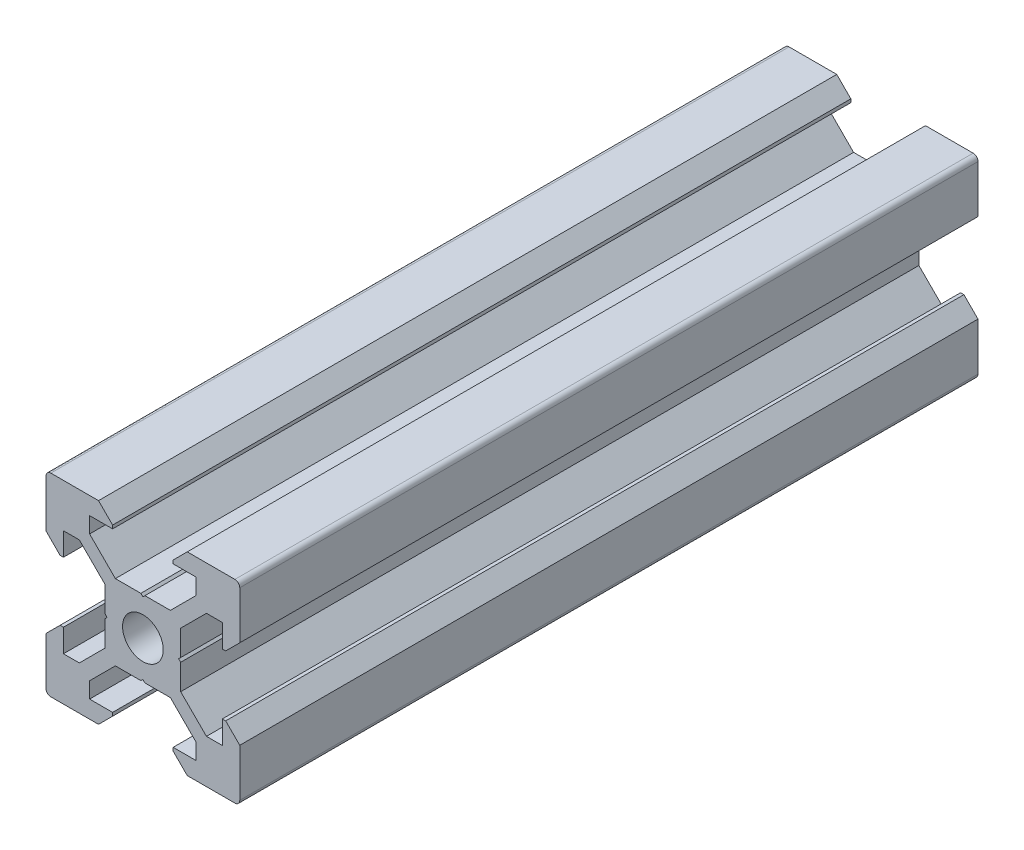
SolidWorks part; units mm, degrees
material "6061-T6 (SS)"
ref_plane "Front Plane" through (0, 0, 0) normal (0, 0, 1) x (1, 0, 0)
ref_plane "Top Plane" through (0, 0, 0) normal (0, 1, 0) x (1, 0, 0)
ref_plane "Right Plane" through (0, 0, 0) normal (1, 0, 0) x (0, 0, -1)
sketch "Sketch1" plane through (0, 0, 0) normal (0, 0, 1) x (1, 0, 0)
  line L1 (9.5, -10) -> (-9.5, -10)
  line L2 (10, -9.5) -> (10, 9.5)
  line L3 (9.5, 10) -> (-9.5, 10)
  line L4 (-10, -9.5) -> (-10, 9.5)
  line L5 (10, -10) -> (-10, 10) construction
  line L6 (10, 10) -> (-10, -10) construction
  circle A0 centre (0, 0) radius 2.1
  arc A1 (-9.5, 10) -> (-10, 9.5) centre (-9.5, 9.5) ccw
  arc A2 (10, 9.5) -> (9.5, 10) centre (9.5, 9.5) ccw
  arc A3 (9.5, -10) -> (10, -9.5) centre (9.5, -9.5) ccw
  arc A4 (-9.5, -10) -> (-10, -9.5) centre (-9.5, -9.5) cw
  point P0 (0, 0)
  line B0 (0, 0) -> (0, 10) construction
  line B1 (0, 3.69) -> (-0.21, 3.9)
  line B2 (-0.21, 3.9) -> (-2.8393, 3.9)
  line B3 (-2.8393, 3.9) -> (-5.5, 6.5607)
  line B4 (-5.5, 6.5607) -> (-5.5, 8.2)
  line B5 (-5.5, 8.2) -> (-3.125, 8.2)
  line B6 (-3.125, 8.2) -> (-3.125, 8.545)
  line B7 (-3.125, 8.545) -> (-4.58, 10)
  line B8 (-4.58, 10) -> (4.58, 10)
  line B9 (0, 0) -> (-5.9132, 5.9132) construction
  line B10 (3.125, 8.545) -> (4.58, 10)
  line B11 (3.125, 8.2) -> (3.125, 8.545)
  line B12 (5.5, 8.2) -> (3.125, 8.2)
  line B13 (5.5, 6.5607) -> (5.5, 8.2)
  line B14 (2.8393, 3.9) -> (5.5, 6.5607)
  line B15 (0.21, 3.9) -> (2.8393, 3.9)
  line B16 (0, 3.69) -> (0.21, 3.9)
  line B17 (0, 0) -> (-10, 0) construction
  line B18 (-3.69, 0) -> (-3.9, -0.21)
  line B19 (-3.9, -0.21) -> (-3.9, -2.8393)
  line B20 (-3.9, -2.8393) -> (-6.5607, -5.5)
  line B21 (-6.5607, -5.5) -> (-8.2, -5.5)
  line B22 (-8.2, -5.5) -> (-8.2, -3.125)
  line B23 (-8.2, -3.125) -> (-8.545, -3.125)
  line B24 (-8.545, -3.125) -> (-10, -4.58)
  line B25 (-10, -4.58) -> (-10, 4.58)
  line B26 (0, 0) -> (-5.9132, -5.9132) construction
  line B27 (-8.545, 3.125) -> (-10, 4.58)
  line B28 (-8.2, 3.125) -> (-8.545, 3.125)
  line B29 (-8.2, 5.5) -> (-8.2, 3.125)
  line B30 (-6.5607, 5.5) -> (-8.2, 5.5)
  line B31 (-3.9, 2.8393) -> (-6.5607, 5.5)
  line B32 (-3.9, 0.21) -> (-3.9, 2.8393)
  line B33 (-3.69, 0) -> (-3.9, 0.21)
  line B34 (0, 0) -> (0, -10) construction
  line B35 (0, -3.69) -> (0.21, -3.9)
  line B36 (0.21, -3.9) -> (2.8393, -3.9)
  line B37 (2.8393, -3.9) -> (5.5, -6.5607)
  line B38 (5.5, -6.5607) -> (5.5, -8.2)
  line B39 (5.5, -8.2) -> (3.125, -8.2)
  line B40 (3.125, -8.2) -> (3.125, -8.545)
  line B41 (3.125, -8.545) -> (4.58, -10)
  line B42 (4.58, -10) -> (-4.58, -10)
  line B43 (0, 0) -> (5.9132, -5.9132) construction
  line B44 (-3.125, -8.545) -> (-4.58, -10)
  line B45 (-3.125, -8.2) -> (-3.125, -8.545)
  line B46 (-5.5, -8.2) -> (-3.125, -8.2)
  line B47 (-5.5, -6.5607) -> (-5.5, -8.2)
  line B48 (-2.8393, -3.9) -> (-5.5, -6.5607)
  line B49 (-0.21, -3.9) -> (-2.8393, -3.9)
  line B50 (0, -3.69) -> (-0.21, -3.9)
  line B51 (0, 0) -> (10, 0) construction
  line B52 (3.69, 0) -> (3.9, 0.21)
  line B53 (3.9, 0.21) -> (3.9, 2.8393)
  line B54 (3.9, 2.8393) -> (6.5607, 5.5)
  line B55 (6.5607, 5.5) -> (8.2, 5.5)
  line B56 (8.2, 5.5) -> (8.2, 3.125)
  line B57 (8.2, 3.125) -> (8.545, 3.125)
  line B58 (8.545, 3.125) -> (10, 4.58)
  line B59 (10, 4.58) -> (10, -4.58)
  line B60 (0, 0) -> (5.9132, 5.9132) construction
  line B61 (8.545, -3.125) -> (10, -4.58)
  line B62 (8.2, -3.125) -> (8.545, -3.125)
  line B63 (8.2, -5.5) -> (8.2, -3.125)
  line B64 (6.5607, -5.5) -> (8.2, -5.5)
  line B65 (3.9, -2.8393) -> (6.5607, -5.5)
  line B66 (3.9, -0.21) -> (3.9, -2.8393)
  line B67 (3.69, 0) -> (3.9, -0.21)
  dimension "D1" = 4.2
  dimension "D3" = 0.5
  dimension "D2" = 20
sketch_block_instance "V Slot 1-4"
sketch_block "V Slot 1" parameters "D1"=10, "D2"=11, "D3"=4.3, "D4"=1.8, "D5"=0.21, "D6"=45, "D7"=9.16, "D8"=1.5, "D9"=6.25
sketch_block_instance "V Slot 1-5"
sketch_block_instance "V Slot 1-6"
sketch_block_instance "V Slot 1-7"
extrude "Boss-Extrude1" add sketch "Sketch1" along normal blind 76.2 contours B67 B52 B53 B54 B55 B56 B57 B58 L2 A2 L3 B10 B11 B12 B13 B14 B15 B16 B1 B2 B3 B4 B5 B6 B7 A1 L4 B27 B28 B29 B30 B31 B32 B33 B18 B19 B20 B21 B22 B23 B24 A4 L1 B44 B45 B46 B47 B48 B49
